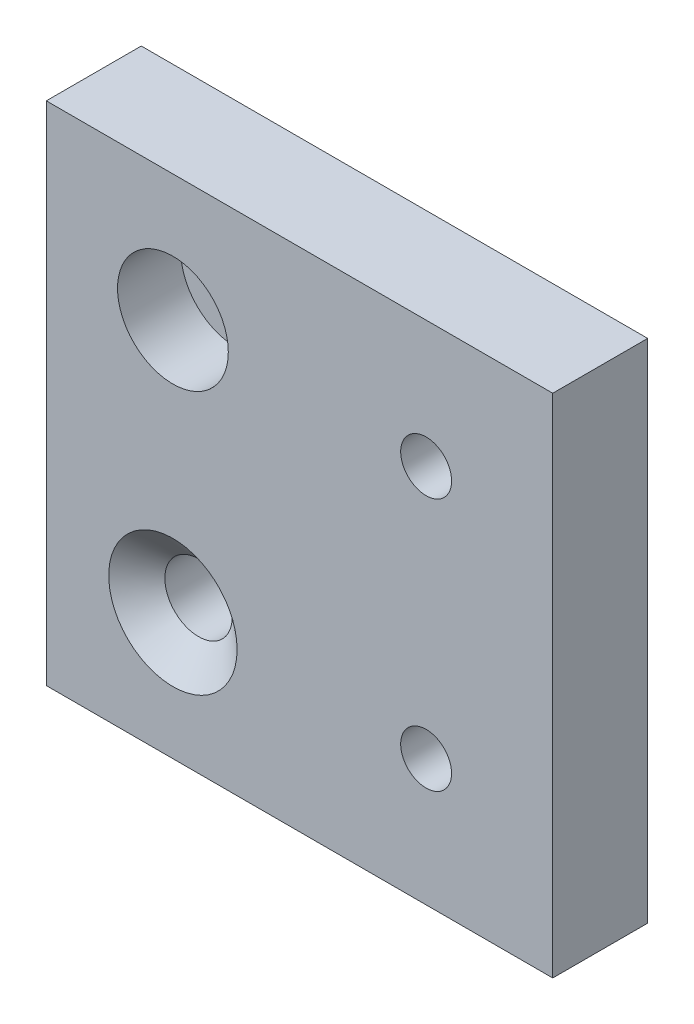
SolidWorks part; units mm, degrees
ref_plane "Front Plane" through (0, 0, 0) normal (0, 0, 1) x (1, 0, 0)
ref_plane "Top Plane" through (0, 0, 0) normal (0, 1, 0) x (1, 0, 0)
ref_plane "Right Plane" through (0, 0, 0) normal (1, 0, 0) x (0, 0, -1)
sketch "Sketch1" plane through (0, 0, 0) normal (0, 0, 1) x (1, 0, 0)
  line L1 (0, 0) -> (50.8, 0)
  line L2 (0, 0) -> (0, 50.8)
  line L3 (0, 50.8) -> (50.8, 50.8)
  line L4 (50.8, 0) -> (50.8, 50.8)
  dimension "D1" = 50.8
extrude "Boss-Extrude1" add sketch "Sketch1" along normal blind 9.525
sketch "Sketch2" plane through (0, 0, 9.525) normal (0, 0, 1) x (1, 0, 0)
  line L1 (0, 0) -> (12.7, 0) construction
  line L2 (0, 0) -> (0, 12.7) construction
  line L3 (0, 12.7) -> (12.7, 12.7) construction
  line L4 (12.7, 0) -> (12.7, 12.7) construction
  line L5 (12.7, 12.7) -> (38.1, 12.7) construction
  line L6 (12.7, 12.7) -> (12.7, 38.1) construction
  line L7 (12.7, 38.1) -> (38.1, 38.1) construction
  line L8 (38.1, 12.7) -> (38.1, 38.1) construction
  line L9 (38.1, 38.1) -> (50.8, 38.1) construction
  line L10 (38.1, 38.1) -> (38.1, 50.8) construction
  line L11 (38.1, 50.8) -> (50.8, 50.8) construction
  line L12 (50.8, 38.1) -> (50.8, 50.8) construction
  dimension "D1" = 25.4
hole_wizard "CBORE for 1/4 Socket Head Cap Screw1" positions "Sketch3" profile "Sketch5" counterbore size "1/4" standard "ANSI Inch" end condition through all
sketch "Sketch3" plane through (0, 0, 9.525) normal (0, 0, 1) x (1, 0, 0)
  point P0 (12.7, 38.1)
sketch "Sketch5" plane through (12.7, 38.1, 9.525) normal (1, 0, 0) x (0, -1, 0)
  line L0 (0, 0) -> (0, 9.525)
  line L1 (0, 9.525) -> (3.3782, 9.525)
  line L3 (3.3782, 9.525) -> (3.3782, 6.35)
  line L4 (3.3782, 6.35) -> (5.5562, 6.35)
  line L5 (5.5562, 6.35) -> (5.5562, 0)
  line L7 (5.5562, 0) -> (0, 0)
  line L11 (0, -6.35) -> (0, 107.95) construction
  dimension "Thru Hole Dia." = 6.7564
  dimension "Thru Hole Depth" = 9.525
  dimension "C'Bore Dia." = 11.1125
  dimension "C'Bore Depth" = 6.35
hole_wizard "1/4-20 Tapped Hole1" positions "Sketch6" profile "Sketch7" tap size "1/4-20" standard "ANSI Inch" end condition through all
sketch "Sketch6" plane through (0, 0, 9.525) normal (0, 0, 1) x (1, 0, 0)
  point P0 (38.1, 38.1)
  point P4 (38.1, 12.7)
sketch "Sketch7" plane through (38.1, 38.1, 9.525) normal (1, 0, 0) x (0, -1, 0)
  line L0 (0, 0) -> (0, 9.525)
  line L1 (0, 9.525) -> (2.5527, 9.525)
  line L2 (2.5527, 9.525) -> (2.5527, 0)
  line L5 (2.5527, 0) -> (0, 0)
  line L11 (0, -6.35) -> (0, 107.95) construction
  dimension "Thru Tap Drill Dia." = 5.1054
  dimension "Thru Tap Drill Depth" = 9.525
cosmetic thread "Hole Thread1" parameters "D2"=6.35
cosmetic thread "Hole Thread2" parameters "D2"=6.35
hole_wizard "CSK for 1/4 Flat Head Machine Screw (100)1" positions "Sketch8" profile "Sketch9" countersink size "1/4" standard "ANSI Inch" end condition through all
sketch "Sketch8" plane through (0, 0, 9.525) normal (0, 0, 1) x (1, 0, 0)
  point P0 (12.7, 12.7)
sketch "Sketch9" plane through (12.7, 12.7, 9.525) normal (1, 0, 0) x (0, -1, 0)
  line L0 (0, 0) -> (0, 9.525)
  line L1 (0, 9.525) -> (3.3782, 9.525)
  line L2 (3.3782, 9.525) -> (3.3782, 2.5682)
  line L3 (3.3782, 2.5682) -> (6.4389, 0)
  line L5 (6.4389, 0) -> (0, 0)
  line L6 (-3.3782, 2.5682) -> (-6.4389, 0) construction
  line L11 (0, -6.35) -> (0, 107.95) construction
  dimension "Thru Hole Dia." = 6.7564
  dimension "Thru Hole Depth" = 9.525
  dimension "Near C'Sink Dia." = 12.8778
  dimension "Near C'Sink Angle" = 100
